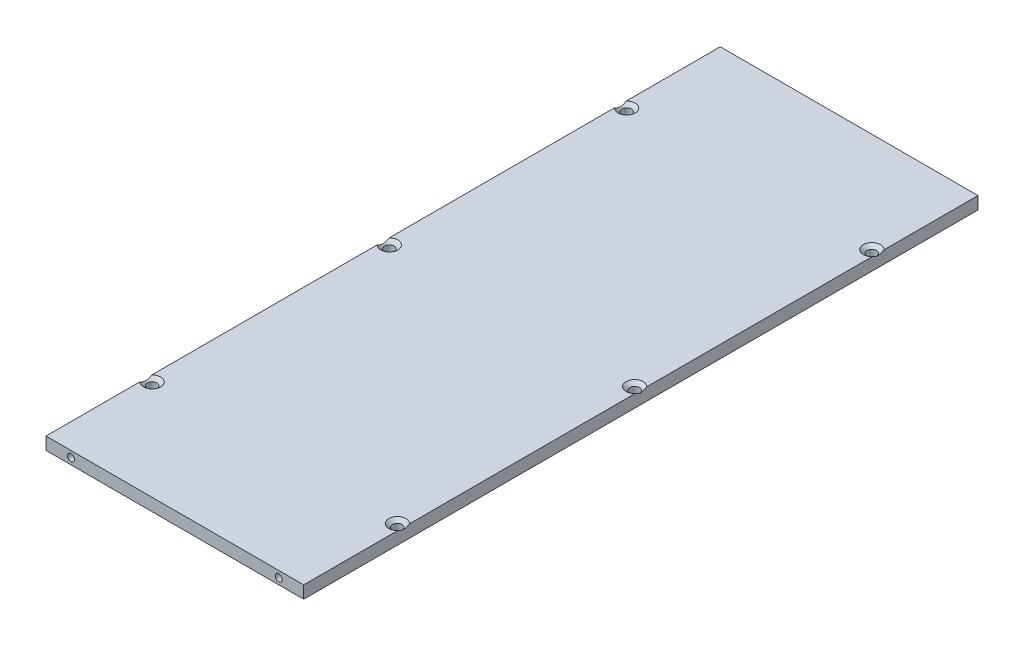
SolidWorks part; units mm, degrees
material "Delrin"
ref_plane "Front Plane" through (0, 0, 0) normal (0, 0, 1) x (1, 0, 0)
ref_plane "Top Plane" through (0, 0, 0) normal (0, 1, 0) x (1, 0, 0)
ref_plane "Right Plane" through (0, 0, 0) normal (1, 0, 0) x (0, 0, -1)
sketch "Sketch1" plane through (0, 0, 0) normal (0, 1, 0) x (1, 0, 0)
  line L1 (-32.766, 85.725) -> (32.766, 85.725)
  line L2 (-32.766, 85.725) -> (-32.766, -85.725)
  line L3 (-32.766, -85.725) -> (32.766, -85.725)
  line L4 (32.766, 85.725) -> (32.766, -85.725)
  dimension "D1" = 32.766
  dimension "D2" = 171.45
  dimension "D3" = 85.725
  dimension "D4" = 65.532
extrude "Extrude1" add sketch "Sketch1" along normal blind 3.175
hole_wizard "Tap Drill for #2 Tap1" positions "3DSketch1" profile "Sketch2" hole size "#2-56" standard "Ansi Inch"
sketch3d "3DSketch1"
  line L0 (-32.766, 3.175, 85.725) -> (32.766, 3.175, 85.725) construction
  line L1 (32.766, 3.175, 85.725) -> (32.766, 0, 85.725) construction
  line L2 (-32.766, 3.175, 85.725) -> (-32.766, 0, 85.725) construction
  point P0 (-26.416, 1.5875, 85.725)
  point P2 (26.416, 1.5875, 85.725)
  dimension "D1" = 1.5875
  dimension "D2" = 1.5875
  dimension "D3" = 6.35
  dimension "D4" = 6.35
sketch "Sketch2" plane through (-26.416, 1.5875, 85.725) normal (1, 0, 0) x (0, -1, 0)
  line L0 (0, 0) -> (0, 6.8842)
  line L1 (0, 6.8842) -> (0.889, 6.35)
  line L2 (0.889, 6.35) -> (0.889, 0)
  line L5 (0.889, 0) -> (0, 0)
  line L10 (0, 6.8842) -> (-0.889, 6.35) construction
  line L11 (0, -6.35) -> (0, 107.95) construction
  dimension "Hole Dia." = 1.778
  dimension "Hole Depth" = 6.35
  dimension "Drill Angle" = 118
hole_wizard "Tap Drill for #2 Tap2" positions "3DSketch2" profile "Sketch3" hole size "#2-56" standard "Ansi Inch"
sketch3d "3DSketch2"
  line L0 (32.766, 3.175, -85.725) -> (-32.766, 3.175, -85.725) construction
  line L1 (32.766, 3.175, -85.725) -> (32.766, 0, -85.725) construction
  line L2 (-32.766, 3.175, -85.725) -> (-32.766, 0, -85.725) construction
  point P0 (26.416, 1.5875, -85.725)
  point P2 (-26.416, 1.5875, -85.725)
  dimension "D1" = 1.5875
  dimension "D2" = 1.5875
  dimension "D3" = 6.35
  dimension "D4" = 6.35
sketch "Sketch3" plane through (26.416, 1.5875, -85.725) normal (1, 0, 0) x (0, 1, 0)
  line L0 (0, 0) -> (0, 6.8842)
  line L1 (0, 6.8842) -> (0.889, 6.35)
  line L2 (0.889, 6.35) -> (0.889, 0)
  line L5 (0.889, 0) -> (0, 0)
  line L10 (0, 6.8842) -> (-0.889, 6.35) construction
  line L11 (0, -6.35) -> (0, 107.95) construction
  dimension "Hole Dia." = 1.778
  dimension "Hole Depth" = 6.35
  dimension "Drill Angle" = 118
hole_wizard "CSK for #2 Flat Head Machine Screw (100)1" positions "3DSketch3" profile "Sketch4" countersink size "#2" standard "Ansi Inch" end condition through all
sketch3d "3DSketch3"
  line L0 (-32.766, 3.175, -85.725) -> (-32.766, 3.175, 85.725) construction
  line L1 (32.766, 3.175, 85.725) -> (32.766, 3.175, -85.725) construction
  line L2 (32.766, 3.175, -85.725) -> (-32.766, 3.175, -85.725) construction
  line L3 (-32.766, 3.175, 85.725) -> (32.766, 3.175, 85.725) construction
  point P0 (-31.1785, 3.175, -60.325)
  point P2 (-31.1785, 3.175, 0)
  point P4 (-31.1785, 3.175, 60.325)
  point P6 (31.1785, 3.175, 60.325)
  point P8 (31.1785, 3.175, 0)
  point P10 (31.1785, 3.175, -60.325)
  dimension "D1" = 1.5875
  dimension "D2" = 1.5875
  dimension "D3" = 85.725
  dimension "D4" = 25.4
  dimension "D5" = 25.4
sketch "Sketch4" plane through (-31.1785, 3.175, -60.325) normal (1, 0, 0) x (0, 0, 1)
  line L0 (0, 0) -> (0, 3.175)
  line L1 (0, 3.175) -> (1.2192, 3.175)
  line L2 (1.2192, 3.175) -> (1.2192, 0.8099)
  line L3 (1.2192, 0.8099) -> (2.1844, 0)
  line L5 (2.1844, 0) -> (0, 0)
  line L6 (-1.2192, 0.8099) -> (-2.1844, 0) construction
  line L11 (0, -6.35) -> (0, 107.95) construction
  dimension "Thru Hole Dia." = 2.4384
  dimension "Thru Hole Depth" = 3.175
  dimension "Near C'Sink Dia." = 4.3688
  dimension "Near C'Sink Angle" = 100
